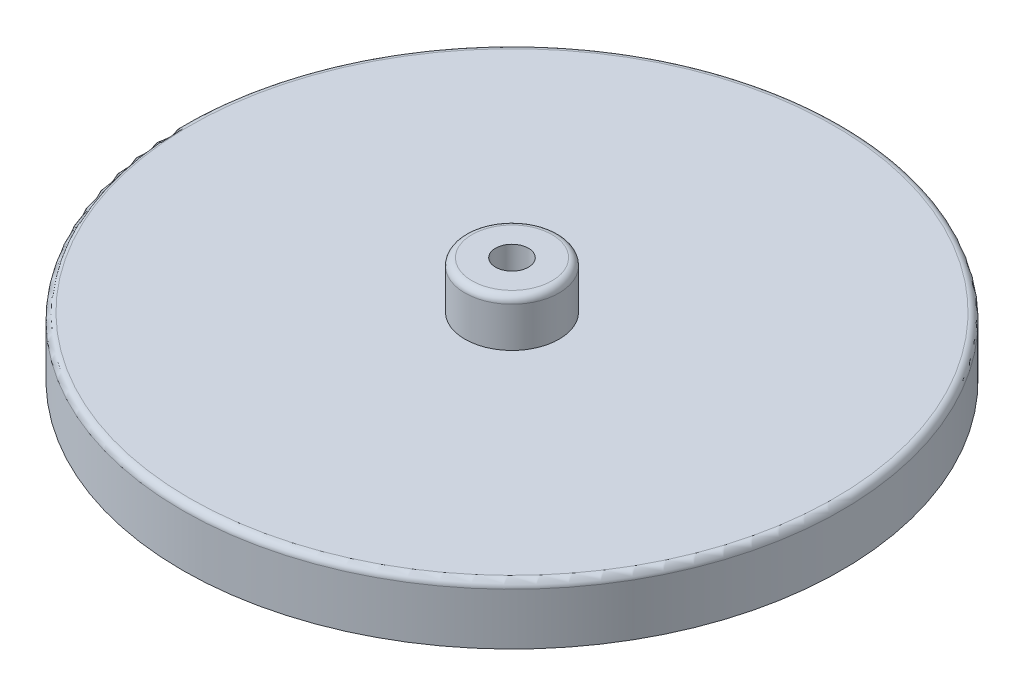
SolidWorks part; units mm, degrees
ref_plane "Front Plane" through (0, 0, 0) normal (0, 0, 1) x (1, 0, 0)
ref_plane "Top Plane" through (0, 0, 0) normal (0, 1, 0) x (1, 0, 0)
ref_plane "Right Plane" through (0, 0, 0) normal (1, 0, 0) x (0, 0, -1)
sketch "Sketch1" plane through (0, 0, 0) normal (0, 1, 0) x (1, 0, 0)
  circle A0 centre (0, 0) radius 35.56
  dimension "D1" = 71.12
extrude "Boss-Extrude1" add sketch "Sketch1" along normal blind 6.35
sketch "Sketch2" plane through (0, 6.35, 0) normal (0, 1, 0) x (1, 0, 0)
  circle A0 centre (0, 0) radius 5.08
  dimension "D1" = 10.16
extrude "Boss-Extrude2" add sketch "Sketch2" along normal blind 5.08
sketch "Sketch3" plane through (0, 11.43, 0) normal (0, 1, 0) x (1, 0, 0)
  circle A0 centre (0, 0) radius 1.778
  dimension "D1" = 3.556
extrude "Cut-Extrude1" cut sketch "Sketch3" against normal through all
sketch "Sketch4" plane through (0, 0, 0) normal (0, -1, 0) x (1, 0, 0)
  circle A0 centre (0, 0) radius 3.556
  dimension "D1" = 7.112
extrude "Cut-Extrude2" cut sketch "Sketch4" against normal blind 2.54
fillet "Fillet1" radius 0.762 1 edges at (0, 11.43, 5.08)
fillet "Fillet2" radius 0.762 1 edges at (0, 6.35, 35.56)
